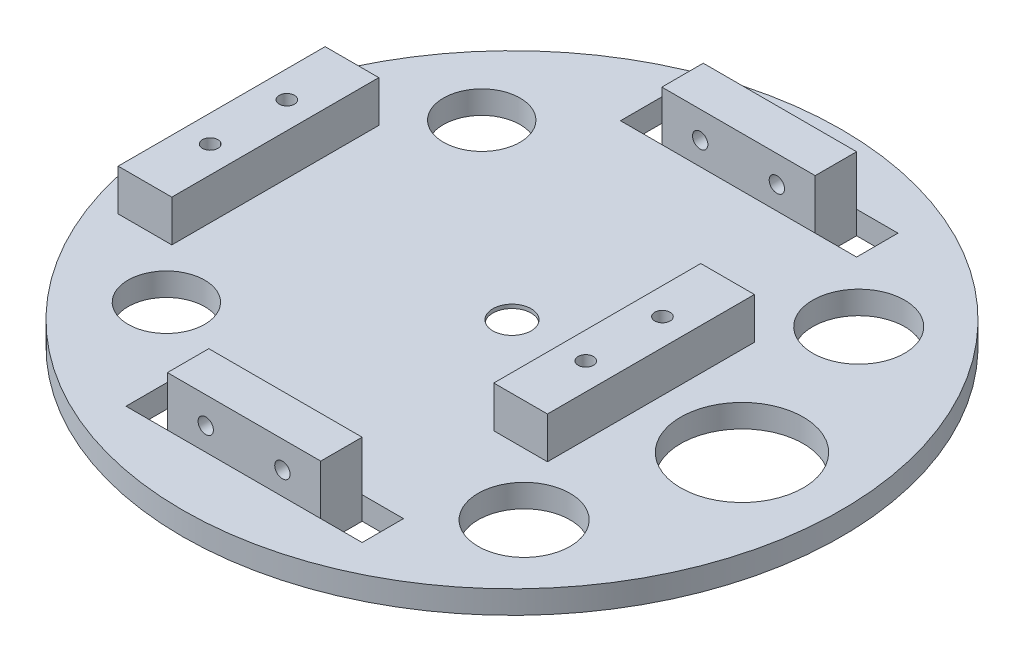
SolidWorks part; units mm, degrees
ref_plane "Alzado" through (0, 0, 0) normal (0, 0, 1) x (1, 0, 0)
ref_plane "Planta" through (0, 0, 0) normal (0, 1, 0) x (1, 0, 0)
ref_plane "Vista lateral" through (0, 0, 0) normal (1, 0, 0) x (0, 0, -1)
sketch "Croquis1" plane through (0, 0, 0) normal (0, 1, 0) x (1, 0, 0)
  line L16 (4.8544, 7.3027) -> (11.0228, 9.3624)
  line L17 (-15.2767, -29.3089) -> (-9.8767, -29.3089)
  line L18 (-15.2767, -29.3089) -> (-15.2767, -34.7089)
  line L19 (-15.2767, -34.7089) -> (-9.8767, -34.7089)
  line L20 (-9.8767, -29.3089) -> (-9.8767, -34.7089)
  line L21 (10.1233, -29.3089) -> (15.5233, -29.3089)
  line L22 (10.1233, -29.3089) -> (10.1233, -34.7089)
  line L23 (10.1233, -34.7089) -> (15.5233, -34.7089)
  line L24 (15.5233, -29.3089) -> (15.5233, -34.7089)
  line L25 (-15.2767, 35.1911) -> (-9.8767, 35.1911)
  line L26 (-15.2767, 35.1911) -> (-15.2767, 29.7911)
  line L27 (-15.2767, 29.7911) -> (-9.8767, 29.7911)
  line L28 (-9.8767, 35.1911) -> (-9.8767, 29.7911)
  line L29 (10.1233, 35.1911) -> (15.5233, 35.1911)
  line L30 (10.1233, 35.1911) -> (10.1233, 29.7911)
  line L31 (10.1233, 29.7911) -> (15.5233, 29.7911)
  line L32 (15.5233, 35.1911) -> (15.5233, 29.7911)
  line L33 (8.599, 0.7996) -> (13.467, 5.1118)
  line L34 (4.8381, -6.8506) -> (11.0066, -8.9103)
  line L35 (8.5977, -0.3561) -> (13.4657, -4.6683)
  line L36 (-3.6676, -7.4187) -> (-2.3671, -13.7906)
  line L37 (3.8366, -7.4274) -> (2.5361, -13.7992)
  line L38 (-8.4125, -0.3366) -> (-13.2804, -4.6488)
  line L39 (-4.6679, -6.8397) -> (-10.8363, -8.8994)
  line L40 (-4.6516, 7.3137) -> (-10.82, 9.3733)
  line L41 (-8.4112, 0.8191) -> (-13.2791, 5.1313)
  line L42 (3.8542, 7.8818) -> (2.5537, 14.2536)
  line L43 (-3.65, 7.8904) -> (-2.3495, 14.2622)
  circle A7 centre (0.1337, 0.2313) radius 42.9895
  circle A8 centre (30.1233, 0.2411) radius 8
  circle A9 centre (23.5266, 22.0651) radius 6
  circle A10 centre (-24.3901, 20.8103) radius 5
  circle A12 centre (-24.3927, -20.328) radius 5.0001
  circle A13 centre (23.5266, -21.5828) radius 6
  arc A14 (4.8544, 7.3027) -> (3.8542, 7.8818) centre (0.0933, 0.2315) ccw
  arc A15 (13.467, 5.1118) -> (11.0228, 9.3624) centre (11.8206, 6.9931) ccw
  arc A16 (11.0066, -8.9103) -> (13.4657, -4.6683) centre (11.8126, -6.5438) ccw
  arc A17 (-2.3671, -13.7906) -> (2.5361, -13.7992) centre (0.0853, -13.3054) ccw
  arc A18 (-13.2804, -4.6488) -> (-10.8363, -8.8994) centre (-11.634, -6.5301) ccw
  arc A19 (-10.82, 9.3733) -> (-13.2791, 5.1313) centre (-11.6261, 7.0069) ccw
  arc A20 (2.5537, 14.2536) -> (-2.3495, 14.2622) centre (0.1012, 13.7685) ccw
  arc A21 (-3.65, 7.8904) -> (-4.6516, 7.3137) centre (0.0933, 0.2315) ccw
  arc A22 (-8.4112, 0.8191) -> (-8.4125, -0.3366) centre (0.0933, 0.2315) ccw
  arc A23 (-4.6679, -6.8397) -> (-3.6676, -7.4187) centre (0.0933, 0.2315) ccw
  arc A24 (3.8366, -7.4274) -> (4.8381, -6.8506) centre (0.0933, 0.2315) ccw
  arc A25 (8.5977, -0.3561) -> (8.599, 0.7996) centre (0.0933, 0.2315) ccw
  point P65 (0.0933, 0.2315)
  dimension "D1" = 6
extrude "Saliente-Extruir1" add sketch "Croquis1" along normal blind 2.5 contours A7 A25 L35 A16 L34 A24 L37 A17 L36 A23 L39 A18 L38 A22 L41 A19 L40 A21 L43 A20 L42 A14 L16 A15 L33 A13 A12 A10 A9 A8 L29 L32 L31 L30 L25 L28 L27 L26 L21 L24 L23 L22
sketch "Croquis2" plane through (0, 2.5, 0) normal (0, 1, 0) x (1, 0, 0)
  line L0 (-15.2767, 35.1911) -> (-15.2767, 29.7911) construction
  line L1 (-15.2767, 35.1911) -> (-9.8767, 35.1911) construction
  line L2 (-9.8767, 35.1911) -> (-9.8767, 29.7911) construction
  line L3 (-15.2767, 29.7911) -> (-9.8767, 29.7911) construction
  line L4 (10.1233, 29.7911) -> (15.5233, 29.7911) construction
  line L5 (10.1233, 35.1911) -> (10.1233, 29.7911) construction
  line L6 (10.1233, 35.1911) -> (15.5233, 35.1911) construction
  line L7 (15.5233, 35.1911) -> (15.5233, 29.7911) construction
  line L8 (10.1233, -29.3089) -> (15.5233, -29.3089) construction
  line L9 (15.5233, -29.3089) -> (15.5233, -34.7089) construction
  line L10 (10.1233, -34.7089) -> (15.5233, -34.7089) construction
  line L11 (10.1233, -29.3089) -> (10.1233, -34.7089) construction
  line L12 (-9.8767, -29.3089) -> (-9.8767, -34.7089) construction
  line L13 (-15.2767, -29.3089) -> (-9.8767, -29.3089) construction
  line L14 (-15.2767, -29.3089) -> (-15.2767, -34.7089) construction
  line L15 (-15.2767, -34.7089) -> (-9.8767, -34.7089) construction
  line L16 (-15.2767, -34.7089) -> (-9.8767, -34.7089)
  line L17 (-15.2767, -29.3089) -> (-15.2767, -34.7089)
  line L18 (-15.2767, -29.3089) -> (-9.8767, -29.3089)
  line L19 (-9.8767, -29.3089) -> (-9.8767, -34.7089)
  line L20 (10.1233, -29.3089) -> (10.1233, -34.7089)
  line L21 (10.1233, -34.7089) -> (15.5233, -34.7089)
  line L22 (15.5233, -29.3089) -> (15.5233, -34.7089)
  line L23 (10.1233, -29.3089) -> (15.5233, -29.3089)
  line L24 (10.1233, 35.1911) -> (15.5233, 35.1911)
  line L25 (10.1233, 35.1911) -> (10.1233, 29.7911)
  line L26 (10.1233, 29.7911) -> (15.5233, 29.7911)
  line L27 (-15.2767, 29.7911) -> (-9.8767, 29.7911)
  line L28 (-9.8767, 35.1911) -> (-9.8767, 29.7911)
  line L29 (-15.2767, 35.1911) -> (-9.8767, 35.1911)
  line L30 (-15.2767, 35.1911) -> (-15.2767, 29.7911)
  line L31 (15.5233, 35.1911) -> (15.5233, 29.7911)
  circle A0 centre (-24.3901, 20.8103) radius 5 construction
  circle A1 centre (0.1337, 0.2313) radius 42.9895
  circle A2 centre (0.1337, 0.2313) radius 42.9895
  circle A3 centre (23.5266, 22.0651) radius 6 construction
  circle A4 centre (30.1233, 0.2411) radius 8 construction
  circle A5 centre (23.5266, -21.5828) radius 6 construction
  circle A6 centre (-24.3927, -20.328) radius 5.0001 construction
  circle A7 centre (-24.3927, -20.328) radius 5.0001
  circle A8 centre (23.5266, -21.5828) radius 6
  circle A9 centre (30.1233, 0.2411) radius 8
  circle A10 centre (23.5266, 22.0651) radius 6
  circle A11 centre (-24.3901, 20.8103) radius 5
  circle A12 centre (0.1337, 0.2313) radius 2.5
  dimension "D2" = 5
  dimension "D1" = 0
extrude "Saliente-Extruir2" add sketch "Croquis2" along normal blind 0.5
sketch "Croquis3" plane through (0, 3, 0) normal (0, 1, 0) x (1, 0, 0)
  line L0 (10.1233, 35.1911) -> (10.1233, 29.7911) construction
  line L1 (-9.8767, -29.3089) -> (10.1233, -29.3089)
  line L2 (-9.8767, -29.3089) -> (-9.8767, -34.7089)
  line L3 (-9.8767, -34.7089) -> (10.1233, -34.7089)
  line L4 (10.1233, -29.3089) -> (10.1233, -34.7089)
  line L5 (-9.8767, 35.1911) -> (10.1233, 35.1911)
  line L6 (-9.8767, 35.1911) -> (-9.8767, 29.7911)
  line L7 (-9.8767, 29.7911) -> (10.1233, 29.7911)
  line L8 (10.1233, 35.1911) -> (10.1233, 29.7911)
  line L9 (10.1233, 29.7911) -> (15.5233, 29.7911) construction
extrude "Saliente-Extruir3" add sketch "Croquis3" along normal blind 6.5
sketch "Croquis4" plane through (0, 0, 34.7089) normal (0, 0, 1) x (1, 0, 0)
  line L0 (-9.8767, 9.5) -> (10.1233, 9.5) construction
  line L1 (-9.8767, 9.5) -> (-9.8767, 3) construction
  circle A0 centre (-4.8767, 6) radius 1
  circle A1 centre (5.1233, 6) radius 1
  point P6 (-21.6013, 16.152)
  dimension "D4" = 2
  dimension "D1" = 10
  dimension "D2" = 3.5
  dimension "D3" = 5
extrude "Cortar-Extruir1" cut sketch "Croquis4" against normal blind 94.5
sketch "Croquis5" plane through (0, 3, 0) normal (0, 1, 0) x (1, 0, 0)
  line L0 (-37.51, 13.5) -> (-37.51, -13.5)
  line L1 (-37.51, -13.5) -> (-30.51, -13.5)
  line L2 (-30.51, -13.5) -> (-30.51, 13.5)
  line L3 (-30.51, 13.5) -> (-37.51, 13.5)
  line L4 (11.49, 13.5) -> (11.49, -13.5)
  line L5 (11.49, -13.5) -> (18.49, -13.5)
  line L6 (18.49, -13.5) -> (18.49, 13.5)
  line L7 (18.49, 13.5) -> (11.49, 13.5)
  circle A0 centre (-34.01, 5) radius 1
  circle A1 centre (-34.01, -5) radius 1
  circle A2 centre (14.99, 5) radius 1
  circle A3 centre (14.99, -5) radius 1
  point P16 (0, 0)
  point P17 (0, 0)
  point P18 (0, 0)
  point P19 (0, 0)
  point P20 (0, 0)
  point P22 (11.49, 0)
  dimension "D7" = 2
  dimension "D1" = 27
  dimension "D2" = 7
  dimension "D3" = 42
  dimension "D4" = 3.5
  dimension "D5" = 10
  dimension "D6" = 8.5
  dimension "D8" = 3.5
  dimension "D9" = 11.49
extrude "Saliente-Extruir4" add sketch "Croquis5" along normal blind 5.4
